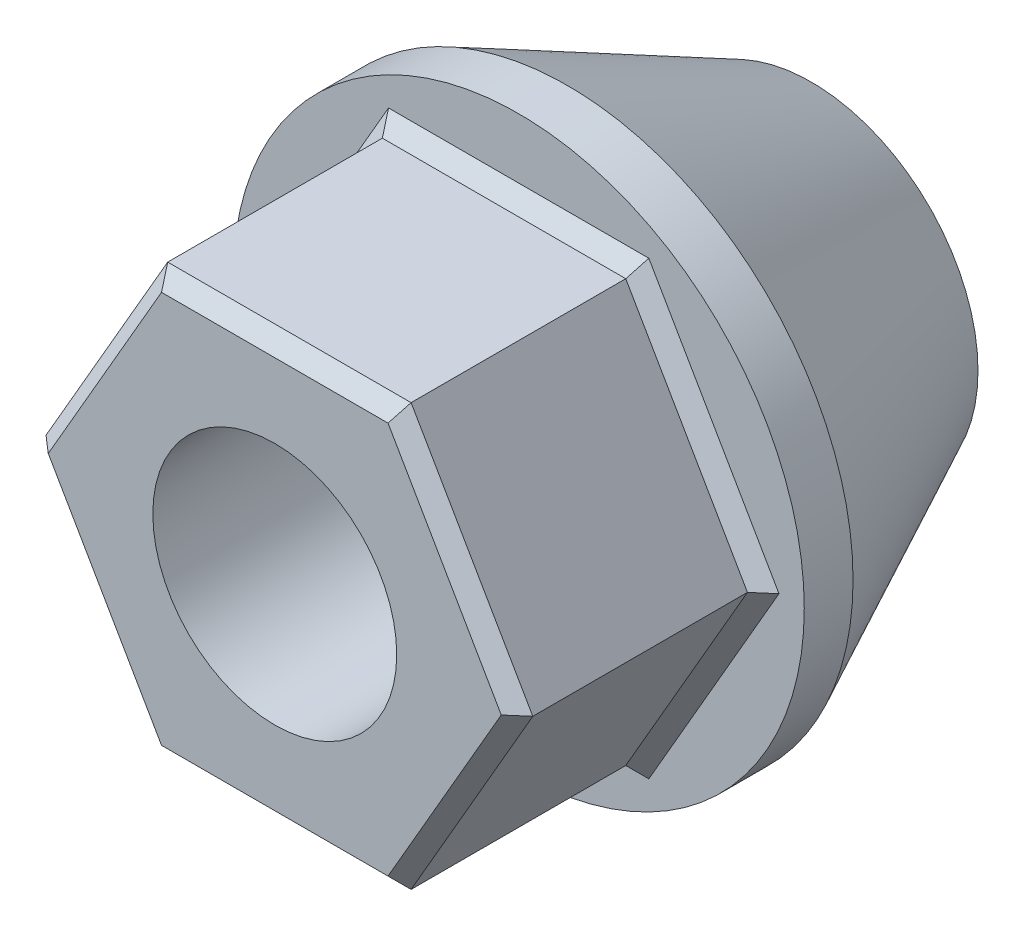
SolidWorks part; units mm, degrees
ref_plane "Front Plane" through (0, 0, 0) normal (0, 0, 1) x (1, 0, 0)
ref_plane "Top Plane" through (0, 0, 0) normal (0, 1, 0) x (1, 0, 0)
ref_plane "Right Plane" through (0, 0, 0) normal (1, 0, 0) x (0, 0, -1)
sketch "Sketch2" plane through (0, 0, 0) normal (0, 0, 1) x (1, 0, 0)
  line L1 (12.6734, 0) -> (6.3367, 10.9755)
  line L2 (6.3367, 10.9755) -> (-6.3367, 10.9755)
  line L3 (-6.3367, 10.9755) -> (-12.6734, 0)
  line L4 (-12.6734, 0) -> (-6.3367, -10.9755)
  line L5 (-6.3367, -10.9755) -> (6.3367, -10.9755)
  line L6 (6.3367, -10.9755) -> (12.6734, 0)
  circle A0 centre (0, 0) radius 10.9755 construction
extrude "Extrude1" add sketch "Sketch2" along normal blind 12.7
sketch "Sketch3" plane through (0, 0, 0) normal (0, 0, -1) x (-1, 0, 0)
  circle A0 centre (0, 0) radius 14.8695
extrude "Extrude2" add sketch "Sketch3" along normal blind 2.54
chamfer "Chamfer1" distance 0.762 angle 45 6 edges at (0, -10.9755, 0) (-9.505, -5.4877, 0) (-9.505, 5.4877, 0) (0, 10.9755, 0) (9.505, 5.4877, 0) (9.505, -5.4877, 0)
chamfer "Chamfer2" distance 0.762 angle 45 6 edges at (0, 10.9755, 12.7) (-9.505, 5.4877, 12.7) (-9.505, -5.4877, 12.7) (0, -10.9755, 12.7) (9.505, -5.4877, 12.7) (9.505, 5.4877, 12.7)
sketch "Sketch5" plane through (0, 0, -2.54) normal (0, 0, -1) x (-1, 0, 0)
  circle A0 centre (0, 0) radius 14.8695
extrude "Extrude3" add sketch "Sketch5" along normal blind 12.7 draft 26
sketch "Sketch4" plane through (0, 0, 12.7) normal (0, 0, 1) x (1, 0, 0)
  circle A0 centre (0, 0) radius 6.35
extrude "Cut-Extrude1" cut sketch "Sketch4" against normal through all
